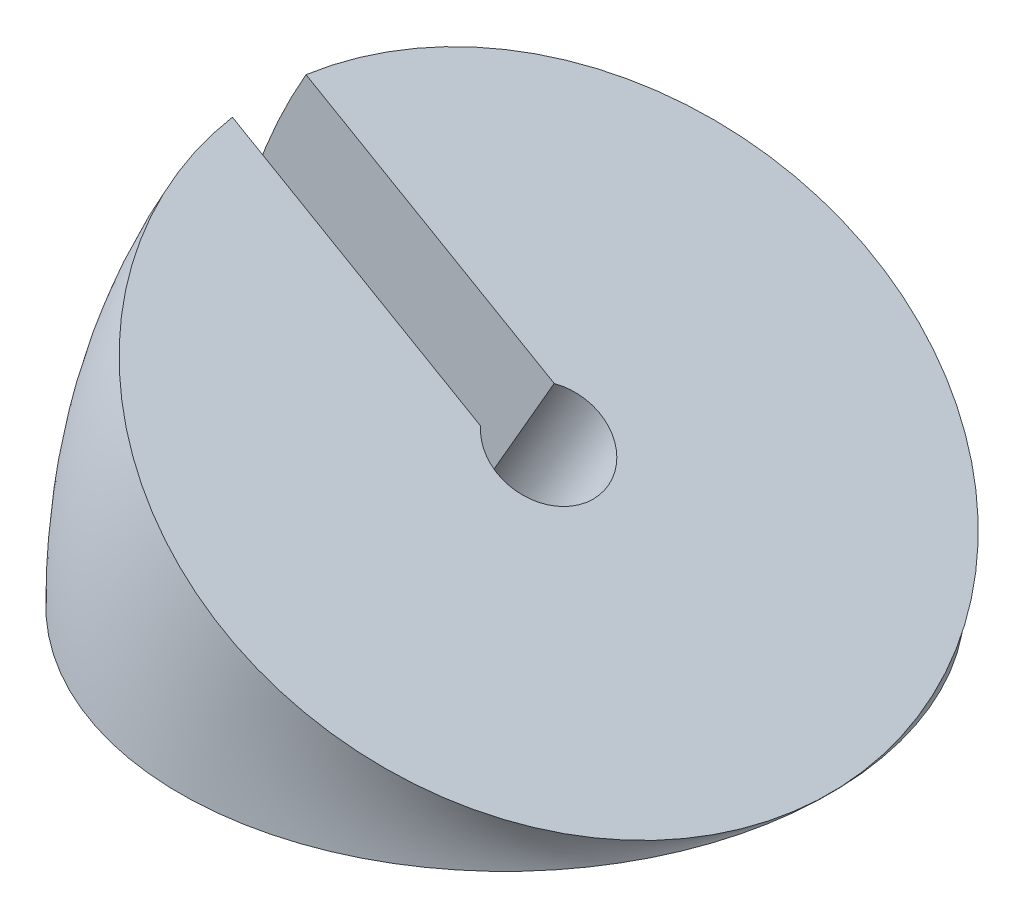
SolidWorks part; units mm, degrees
ref_plane "정면" through (0, 0, 0) normal (0, 0, 1) x (1, 0, 0)
ref_plane "윗면" through (0, 0, 0) normal (0, 1, 0) x (1, 0, 0)
ref_plane "우측면" through (0, 0, 0) normal (1, 0, 0) x (0, 0, -1)
sketch "스케치1" plane through (0, 0, 0) normal (0, 1, 0) x (1, 0, 0)
  circle A2 centre (0, 0) radius 20.05 construction
  circle A3 centre (0, 0) radius 22.05
  dimension "D1" = 40.1
  dimension "D2" = 2
sketch "스케치2" plane through (0, 0, 0) normal (0, 1, 0) x (1, 0, 0)
  line L0 (22.1, 22.2388) -> (22.1, -21.2355) construction
  dimension "D1" = 22.1
revolve "회전8" add sketch "스케치1" angle 30 about L0
sketch "스케치3" plane through (5.525, 9.5696, 0) normal (0.5, 0.866, 0) x (0.866, -0.5, 0)
  line L1 (-2.9608, -2.5) -> (-32.9608, -2.5)
  line L2 (-2.9608, -2.5) -> (-2.9608, 2.5)
  line L3 (-2.9608, 2.5) -> (-32.9608, 2.5)
  line L4 (-32.9608, -2.5) -> (-32.9608, 2.5)
  circle A0 centre (-2.9608, 0) radius 3.5
  point P8 (-2.9608, 0)
  circle M5 centre (-2.9608, 0) radius 22.05
  dimension "D2" = 7
  dimension "D1" = 5
  dimension "D3" = 30
extrude "컷-돌출1" cut sketch "스케치3" against normal through all both contours L1 A0 L3 L2 | L3 A0 L1 L2 | A0 L3 L1 M5
